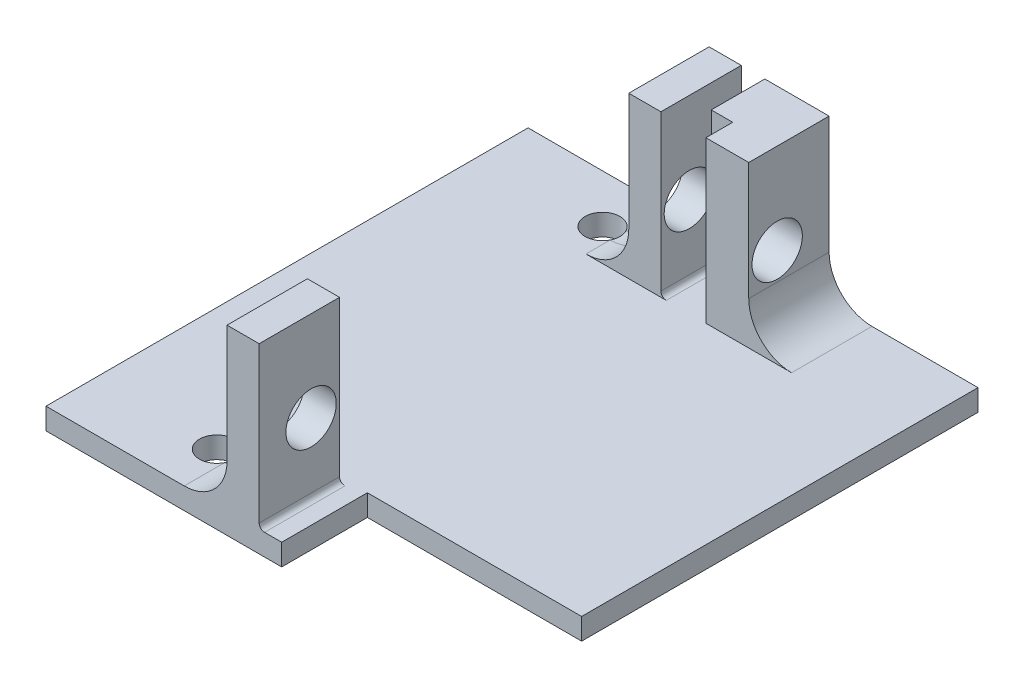
SolidWorks part; units mm, degrees
ref_plane "Front Plane" through (0, 0, 0) normal (0, 0, 1) x (1, 0, 0)
ref_plane "Top Plane" through (0, 0, 0) normal (0, 1, 0) x (1, 0, 0)
ref_plane "Right Plane" through (0, 0, 0) normal (1, 0, 0) x (0, 0, -1)
sketch "Sketch1" plane through (0, 0, 0) normal (0, 1, 0) x (1, 0, 0)
  line L0 (0, 0) -> (0, 45)
  line L1 (0, 45) -> (42, 45)
  line L2 (42, 45) -> (42, 8)
  line L3 (22, 0) -> (0, 0)
  line L4 (22, 0) -> (22, 8)
  line L5 (22, 8) -> (42, 8)
  dimension "D1" = 42
  dimension "D2" = 45
  dimension "D3" = 20
  dimension "D4" = 8
extrude "Boss-Extrude1" add sketch "Sketch1" along normal blind 2
sketch "Sketch2" plane through (0, 2, 0) normal (0, 1, 0) x (1, 0, 0)
  line L0 (16.9, 45) -> (16.9, 37.5)
  line L1 (42, 45) -> (0, 45) construction
  line L2 (0, 0) -> (22, 0) construction
  line L3 (16.9, 0) -> (19.9, 0)
  line L4 (19.9, 0) -> (19.9, 7.5)
  line L5 (19.9, 45) -> (16.9, 45)
  line L6 (21, 45) -> (21, 0) construction
  line L7 (16.9, 37.5) -> (19.9, 37.5)
  line L8 (16.9, 7.5) -> (19.9, 7.5)
  line L9 (0, 22.5) -> (42, 22.5) construction
  line L10 (0, 45) -> (0, 0) construction
  line L11 (22.1, 45) -> (22.1, 40)
  line L12 (16.9, 7.5) -> (16.9, 0)
  line L13 (19.9, 37.5) -> (19.9, 45)
  line L14 (22.1, 40) -> (24.1, 40)
  line L15 (24.1, 40) -> (24.1, 37.5)
  line L16 (24.1, 37.5) -> (28.1, 37.5)
  line L17 (28.1, 37.5) -> (28.1, 45)
  line L18 (22.1, 45) -> (28.1, 45)
  dimension "D1" = 3
  dimension "D2" = 1.1
  dimension "D3" = 30
  dimension "D4" = 1.1
  dimension "D5" = 6
  dimension "D6" = 4
  dimension "D7" = 2.5
extrude "Boss-Extrude2" add sketch "Sketch2" along normal blind 15
sketch "Sketch3" plane through (0, 2, 0) normal (0, 1, 0) x (1, 0, 0)
  line L0 (0, 40.5) -> (42, 40.5) construction
  line L1 (0, 45) -> (0, 0) construction
  line L2 (42, 8) -> (42, 45) construction
  line L3 (0, 22.5) -> (42, 22.5) construction
  line L4 (0, 4.5) -> (42, 4.5) construction
  line L5 (11.45, 45) -> (11.45, 0) construction
  line L6 (16.9, 45) -> (0, 45) construction
  line L7 (0, 0) -> (16.9, 0) construction
  line L8 (19.9, 37.5) -> (19.9, 45) construction
  circle A0 centre (11.45, 40.5) radius 1.625
  circle A1 centre (11.45, 4.5) radius 1.625
  dimension "D3" = 3.25
  dimension "D1" = 36
  dimension "D2" = 18
  dimension "D4" = 8.45
extrude "Cut-Extrude1" cut sketch "Sketch3" against normal up to next
sketch "Sketch4" plane through (16.9, 0, 0) normal (1, 0, 0) x (0, 0, -1)
  line L2 (45, 2) -> (0, 2) construction
  line L3 (45, 2) -> (0, 2)
  line L4 (22.5, 2) -> (22.5, 24.6453) construction
  circle A0 centre (4.845, 8.58) radius 2.35
  circle A1 centre (40.155, 8.58) radius 2.35
  dimension "D2" = 4.7
  dimension "D3" = 35.31
  dimension "D1" = 6.58
extrude "Cut-Extrude2" cut sketch "Sketch4" along normal through all contours A1 | A0
fillet "Fillet1" radius 4 3 edges at (16.9, 2, -3.75) (28.1, 2, -41.25)
fillet "Fillet2" radius 0.5 3 edges at (19.9, 2, -3.75) (22.1, 2, -42.5)
